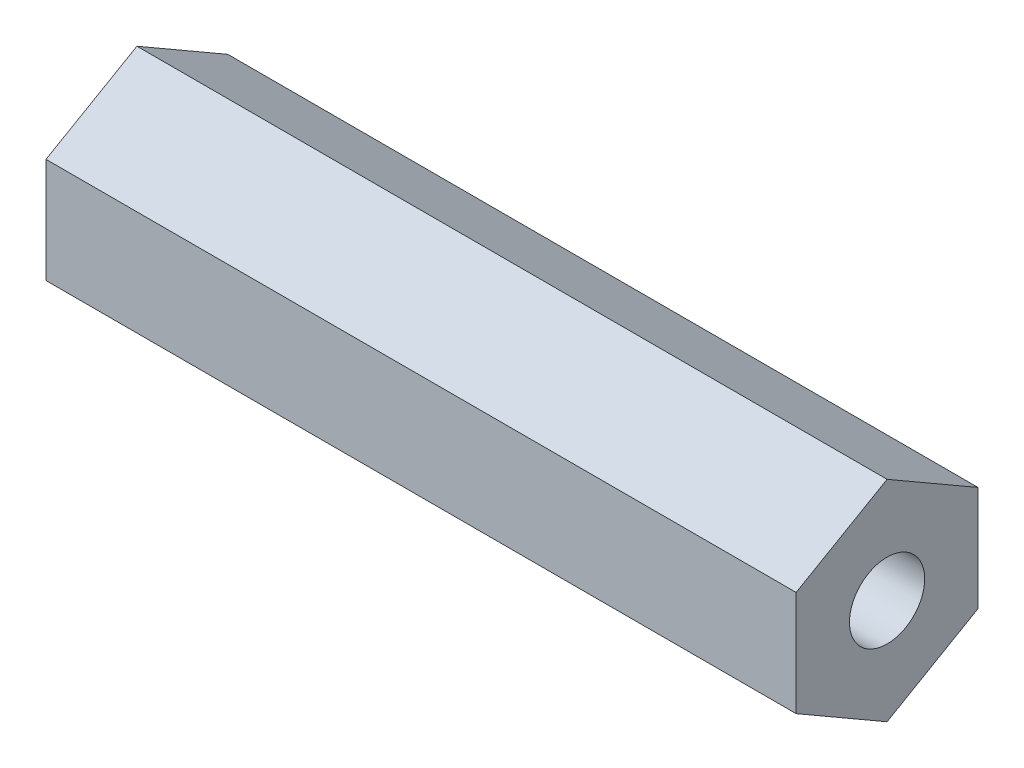
SolidWorks part; units mm, degrees
material "6061-T6 (SS)"
ref_plane "Front Plane" through (0, 0, 0) normal (0, 0, 1) x (1, 0, 0)
ref_plane "Top Plane" through (0, 0, 0) normal (0, 1, 0) x (1, 0, 0)
ref_plane "Right Plane" through (0, 0, 0) normal (1, 0, 0) x (0, 0, -1)
sketch "Sketch2" plane through (0, 0, 0) normal (1, 0, 0) x (0, 0, -1)
  line L1 (0, 7.3323) -> (-6.35, 3.6662)
  line L2 (-6.35, 3.6662) -> (-6.35, -3.6662)
  line L3 (-6.35, -3.6662) -> (0, -7.3323)
  line L4 (0, -7.3323) -> (6.35, -3.6662)
  line L5 (6.35, -3.6662) -> (6.35, 3.6662)
  line L6 (6.35, 3.6662) -> (0, 7.3323)
  circle A0 centre (0, 0) radius 6.35 construction
  circle A1 centre (0, 0) radius 2.6289
  dimension "D1" = 5.2578
  dimension "D2" = 12.7
extrude "Boss-Extrude1" add sketch "Sketch2" along normal blind 52.3875
